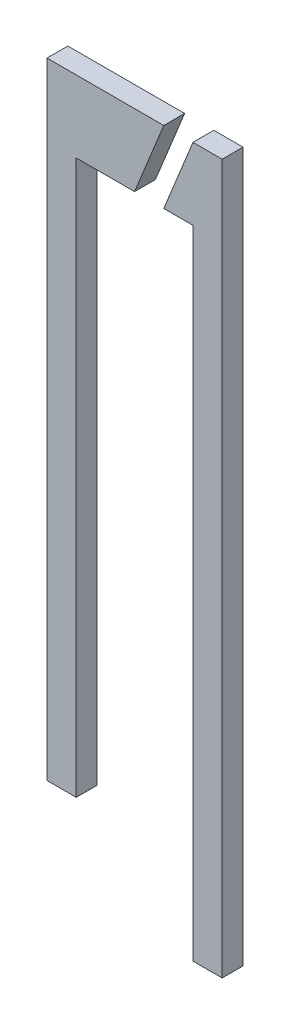
SolidWorks part; units mm, degrees
ref_plane "Ön Düzlem" through (0, 0, 0) normal (0, 0, 1) x (1, 0, 0)
ref_plane "Üst Düzlem" through (0, 0, 0) normal (0, 1, 0) x (1, 0, 0)
ref_plane "Sağ Düzlem" through (0, 0, 0) normal (1, 0, 0) x (0, 0, -1)
sketch "Sketch2" plane through (0, 0, 0) normal (0, 0, 1) x (1, 0, 0)
  line L0 (2.1, -1.725) -> (2.1, 15.275)
  line L1 (2.1, 15.275) -> (1.4, 15.275)
  line L2 (1.4, 15.275) -> (0.7, 13.5512)
  line L3 (0.7, 13.5512) -> (1.4, 13.5512)
  line L4 (1.4, 13.5512) -> (1.4, -1.725)
  line L5 (1.4, -1.725) -> (2.1, -1.725)
  line L6 (0.7, 15.275) -> (0, 13.5512)
  line L7 (0, 13.5512) -> (-1.4, 13.5512)
  line L8 (-1.4, 13.5512) -> (-1.4, 0.275)
  line L9 (-1.4, 0.275) -> (-2.1, 0.275)
  line L10 (-2.1, 0.275) -> (-2.1, 15.275)
  line L11 (-2.1, 15.275) -> (0.7, 15.275)
  line L12 (0, -2.6073) -> (0, 6.9342) construction
  dimension "D1" = 0.7
  dimension "D2" = 17
  dimension "D3" = 15
  dimension "D4" = 0.7
  dimension "D5" = 1.4
  dimension "D6" = 0.7
  dimension "D7" = 0.7
  dimension "D8" = 0.7
  dimension "D9" = 0.7
extrude "Extrude2" add sketch "Sketch2" along normal blind 0.5
